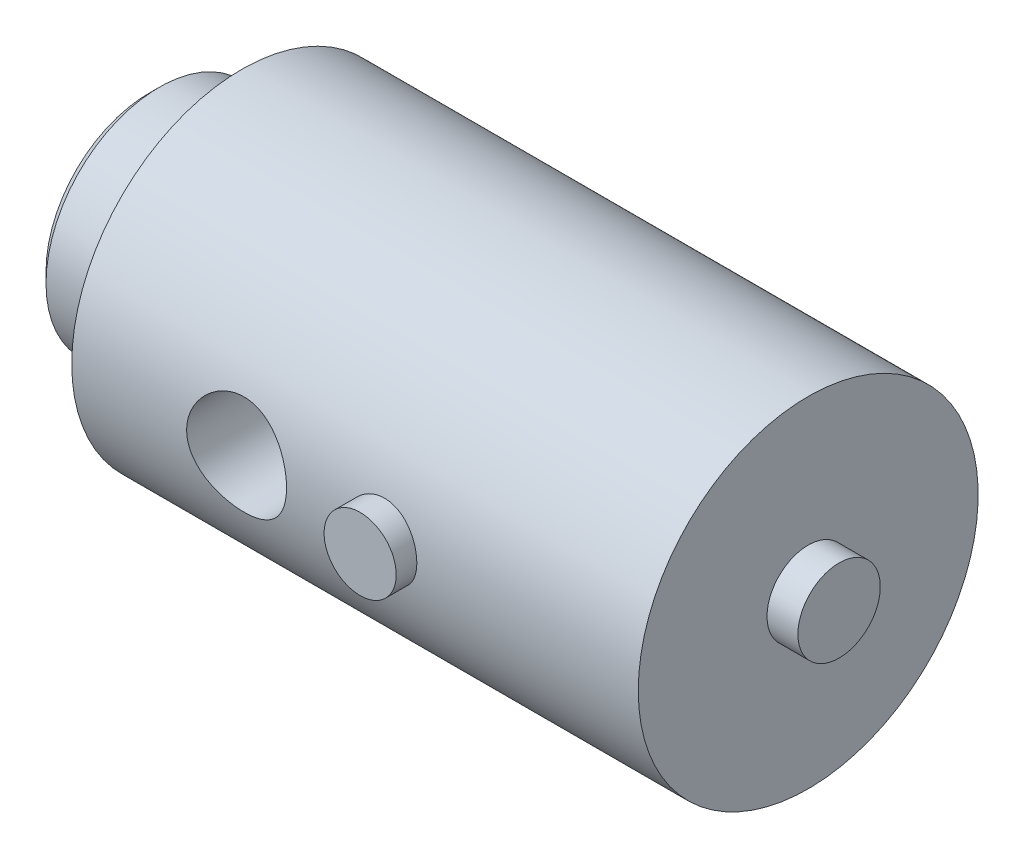
SolidWorks part; units mm, degrees
material "7075-T6 (SN)"
ref_plane "Front Plane" through (0, 0, 0) normal (0, 0, 1) x (1, 0, 0)
ref_plane "Top Plane" through (0, 0, 0) normal (0, 1, 0) x (1, 0, 0)
ref_plane "Right Plane" through (0, 0, 0) normal (1, 0, 0) x (0, 0, -1)
sketch "Sketch1" plane through (0, 0, 0) normal (0, 1, 0) x (1, 0, 0)
  line L0 (0, 0) -> (69.0915, 0) construction
  line L1 (0, 10) -> (0, 6)
  line L2 (1, 11) -> (9, 11)
  line L3 (9, 11) -> (9, 16.5)
  line L4 (9, 16.5) -> (64, 16.5)
  line L5 (64, 16.5) -> (64, 4)
  line L6 (64, 4) -> (67, 4)
  line L7 (67, 4) -> (67, 0)
  line L8 (2, 4) -> (11, 4)
  line L9 (11, 4) -> (11, 0)
  line L10 (1, 11) -> (0, 10)
  line L11 (0, 6) -> (2, 4)
  line L12 (67, 0) -> (11, 0)
  point P4 (0, 11)
  point P11 (0, 4)
  dimension "D1" = 55
  dimension "D2" = 9
  dimension "D3" = 3
  dimension "D4" = 22
  dimension "D5" = 33
  dimension "D6" = 8
  dimension "D7" = 11
  dimension "D8" = 8
revolve "Revolve1" add sketch "Sketch1" angle 360 about L0
ref_plane "Plane1" through (0, 0, 16.5) normal (0, 0, 1) x (1, 0, 0)
sketch "Sketch2" plane through (0, 0, 16.5) normal (0, 0, 1) x (1, 0, 0)
  line L0 (9, 16.5) -> (9, -16.5) construction
  circle A0 centre (25, 0) radius 4.85
  dimension "D1" = 9.7
  dimension "D2" = 16
extrude "Cut-Extrude1" cut sketch "Sketch2" against normal blind 9
sketch "Sketch3" plane through (0, 0, 16.5) normal (0, 0, 1) x (1, 0, 0)
  line L0 (9, 16.5) -> (9, -16.5) construction
  circle A0 centre (39, 0) radius 3.5
  dimension "D1" = 7
  dimension "D2" = 30
extrude "Boss-Extrude1" add sketch "Sketch3" along normal blind 2 and the other way up to next
